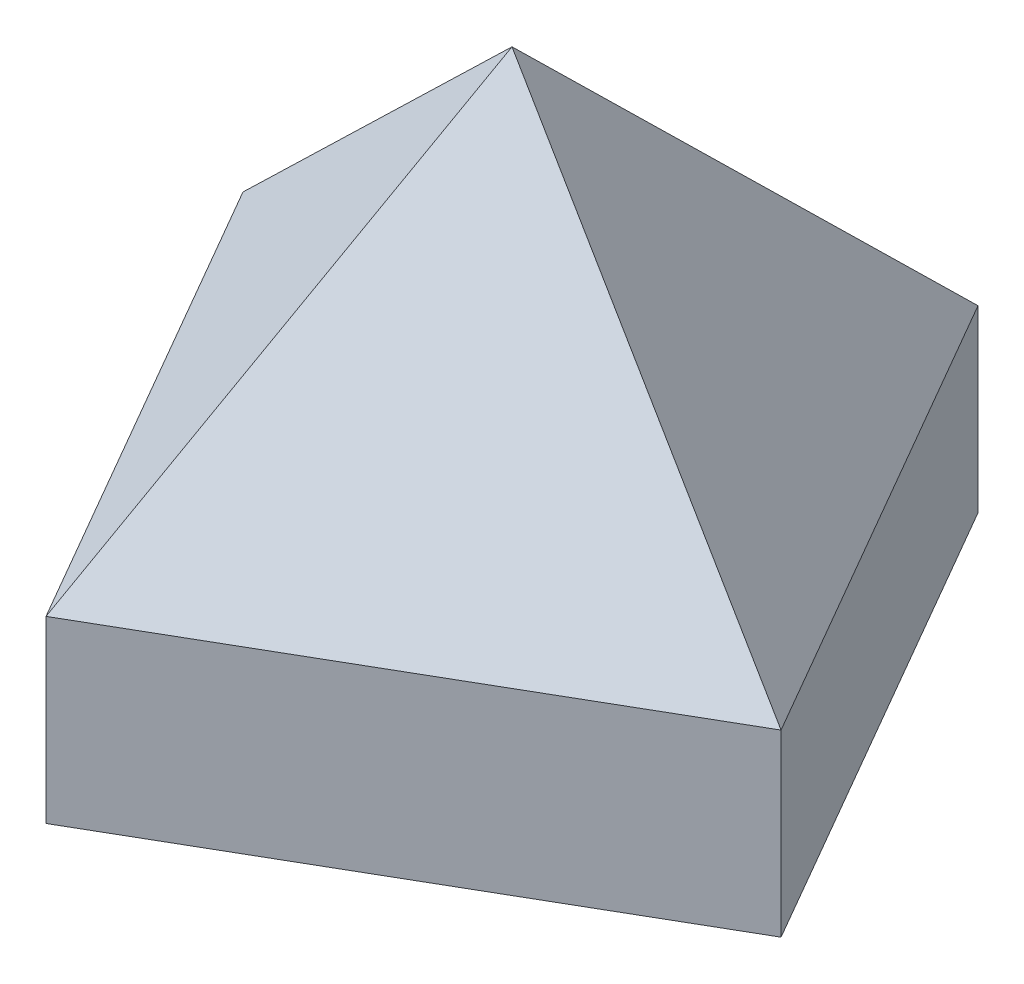
SolidWorks part; units mm, degrees
ref_plane "Front Plane" through (0, 0, 0) normal (0, 0, 1) x (1, 0, 0)
ref_plane "Top Plane" through (0, 0, 0) normal (0, 1, 0) x (1, 0, 0)
ref_plane "Right Plane" through (0, 0, 0) normal (1, 0, 0) x (0, 0, -1)
sketch "Sketch1" plane through (0, 0, 0) normal (0, 1, 0) x (1, 0, 0)
  line L0 (-92.5, -15) -> (-55, -79.9519)
  line L1 (-92.5, -15) -> (-40.1648, -15) construction
  line L2 (-92.5, -15) -> (-157.4519, -52.5)
  line L3 (-157.4519, -52.5) -> (-119.9519, -117.4519)
  line L4 (-55, -79.9519) -> (-119.9519, -117.4519)
  dimension "D1" = 55
  dimension "D2" = 15
  dimension "D3" = 60
  dimension "D4" = 75
  dimension "D5" = 75
extrude "Extrude1" add sketch "Sketch1" along normal blind 75
sketch "Sketch2" plane through (20.8702, 0, 36.1482) normal (0.5, 0, 0.866) x (0.866, 0, -0.5)
  line L0 (-125.1073, 75) -> (-87.6073, 25)
  line L1 (-162.6073, 75) -> (-87.6073, 75) construction
  line L2 (-87.6073, 75) -> (-87.6073, 0) construction
  line L3 (-87.6073, 25) -> (-87.6073, 75)
  line L4 (-87.6073, 75) -> (-125.1073, 75)
  line L5 (-125.1073, 75) -> (-162.6073, 75)
  line L6 (-162.6073, 75) -> (-162.6073, 25)
  line L7 (-162.6073, 75) -> (-162.6073, 0) construction
  line L8 (-162.6073, 25) -> (-125.1073, 75)
  line M2 (-87.6073, 0) -> (-87.6073, 75)
  line M3 (-87.6073, 75) -> (-162.6073, 75)
  line M4 (-162.6073, 75) -> (-162.6073, 0)
  dimension "D1" = 50
  dimension "D2" = 50
extrude "Extrude2" cut sketch "Sketch2" against normal through all contours L8 M4 M3 | L0 M3 M2
sketch "Sketch3" plane through (-140.8221, 0, 81.3037) normal (-0.866, 0, 0.5) x (0.5, 0, 0.866)
  line L0 (41.7404, 25) -> (4.2404, 75)
  line L1 (41.7404, 75) -> (-33.2596, 75) construction
  line L2 (4.2404, 75) -> (41.7404, 75)
  line L4 (41.7404, 75) -> (41.7404, 25)
  line L5 (4.2404, 75) -> (-33.2596, 25)
  line L6 (-33.2596, 25) -> (-33.2596, 75)
  line L7 (-33.2596, 75) -> (4.2404, 75)
extrude "Extrude3" cut sketch "Sketch3" against normal through all contours L7 L6 L5 | L4 L2 L0
sketch "HT" plane through (0, 0, 0) normal (0, 1, 0) x (1, 0, 0)
  line L0 (0, 0) -> (-99.3921, -172.1522)
  line L1 (0, 0) -> (-227.1421, 0) construction
  dimension "D1" = 60
sketch "VT" plane through (0, 0, 0) normal (0, 0, 1) x (1, 0, 0)
  line L0 (0, 0) -> (-161.961, 114.3513)
ref_plane "Oblique Plane" through (0, 0, 0) normal (0.5472, 0.7751, 0.3159) x (-0.837, 0.5067, 0.2066)
